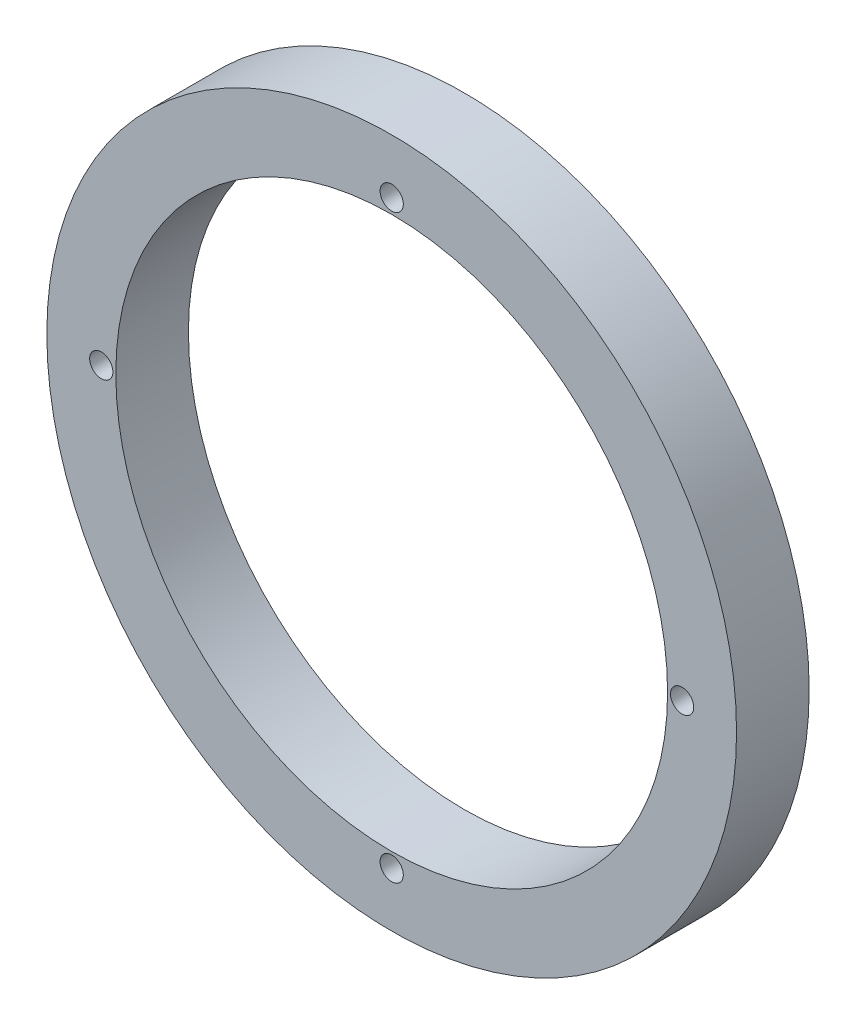
SolidWorks part; units mm, degrees
ref_plane "Plan de face" through (0, 0, 0) normal (0, 0, 1) x (1, 0, 0)
ref_plane "Plan de dessus" through (0, 0, 0) normal (0, 1, 0) x (1, 0, 0)
ref_plane "Plan de droite" through (0, 0, 0) normal (1, 0, 0) x (0, 0, -1)
sketch "Esquisse1" plane through (0, 0, 0) normal (0, 0, 1) x (1, 0, 0)
  line L0 (0, 0) -> (0, 4)
  circle A0 centre (0, 0) radius 3.8
  circle A1 centre (0, 0) radius 4.75
  circle A2 centre (0, 4) radius 0.16
  circle A3 centre (4, 0) radius 0.16
  circle A4 centre (0, -4) radius 0.16
  circle A5 centre (-4, 0) radius 0.16
  point P15 (0, 0)
  dimension "D1" = 4
extrude "Boss.-Extru.1" add sketch "Esquisse1" along normal blind 1
